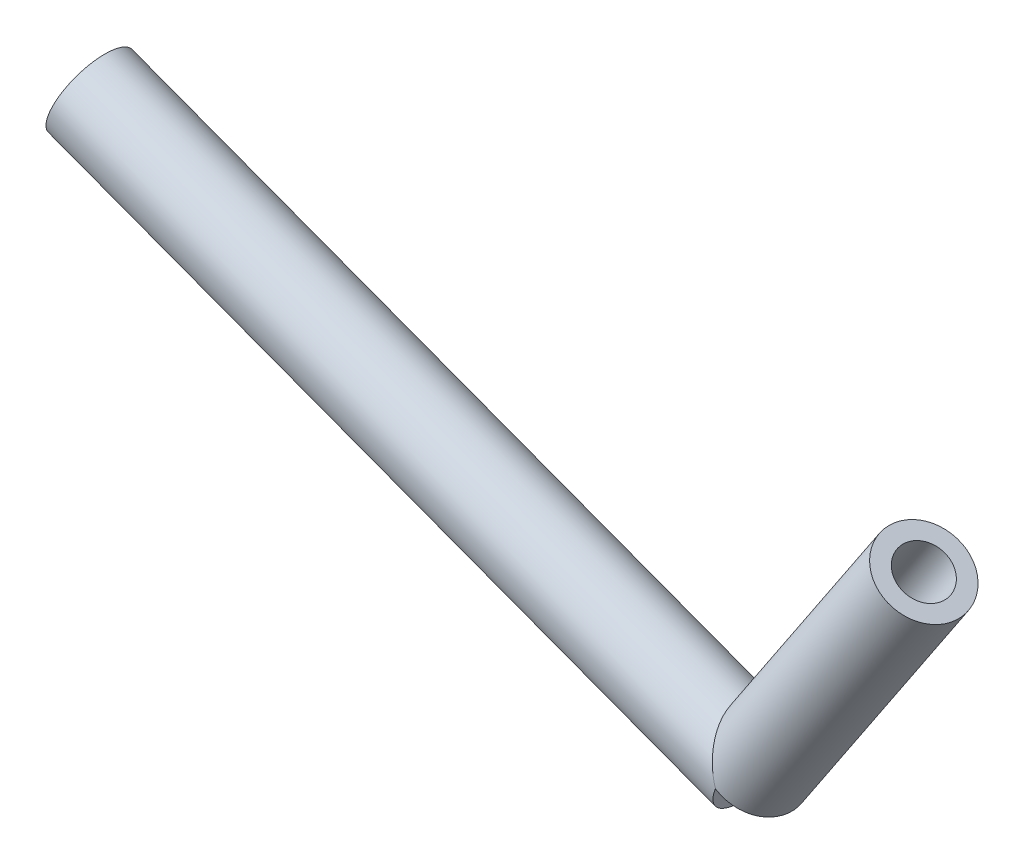
SolidWorks part; units mm, degrees
ref_plane "Front Plane" through (0, 0, 0) normal (0, 0, 1) x (1, 0, 0)
ref_plane "Top Plane" through (0, 0, 0) normal (0, 1, 0) x (1, 0, 0)
ref_plane "Right Plane" through (0, 0, 0) normal (1, 0, 0) x (0, 0, -1)
sketch "Sketch1" plane through (0, 0, 0) normal (0, 0, 1) x (1, 0, 0)
  line L0 (-400, 0) -> (0, 0) construction
  line L1 (0, 0) -> (100, 0) construction
  line L2 (-400, 0) -> (0, -150)
  line L3 (0, -150) -> (100, 0)
  point P3 (0, -150)
  dimension "D1" = 400
  dimension "D2" = 100
  dimension "D3" = 150
other "Pipe 33.7 X 4.0(1)"
ref_plane "Plane1" through (-400, 0, 0) normal (0.9363, -0.3511, 0) x (0.3511, 0.9363, 0)
sketch "Sketch11" plane through (-400, 0, 0) normal (0.9363, -0.3511, 0) x (0.3511, 0.9363, 0)
  circle A0 centre (0, 0) radius 15
  circle A1 centre (0, 0) radius 25
  point P3 (0, 25)
  point P5 (-25, 0)
  point P6 (0, -25)
  point P7 (25, 0)
  point P8 (0, 0)
  dimension "In_dia" = 30
  dimension "Out_dia" = 50
